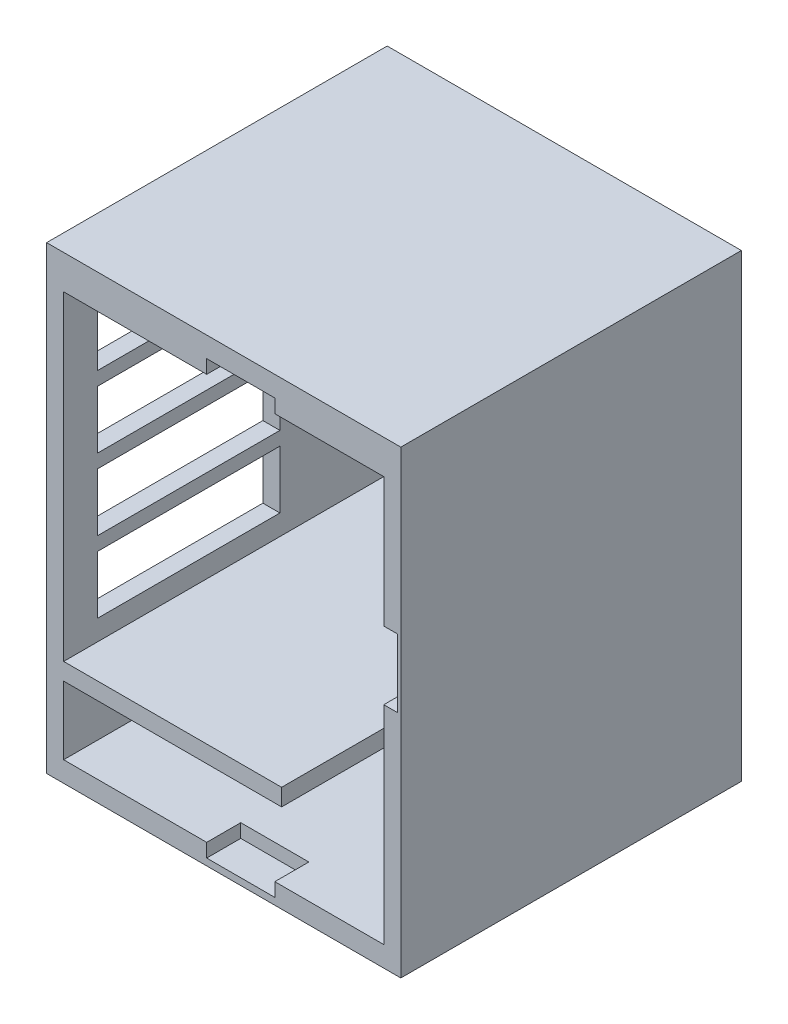
SolidWorks part; units mm, degrees
ref_plane "前基準面" through (0, 0, 0) normal (0, 0, 1) x (1, 0, 0)
ref_plane "上基準面" through (0, 0, 0) normal (0, 1, 0) x (1, 0, 0)
ref_plane "右基準面" through (0, 0, 0) normal (1, 0, 0) x (0, 0, -1)
sketch "草圖1" plane through (0, 0, 0) normal (0, 0, 1) x (1, 0, 0)
  line L5 (-72.8941, 49.2863) -> (31.1059, 49.2863)
  line L6 (-72.8941, 49.2863) -> (-72.8941, -85.7137)
  line L7 (-72.8941, -85.7137) -> (31.1059, -85.7137)
  line L8 (31.1059, 49.2863) -> (31.1059, -85.7137)
  circle A0 centre (-20.8941, -7.7137) radius 47
  dimension "D1" = 94
  dimension "D2" = 52
  dimension "D3" = 104
  dimension "D4" = 135
extrude "填料-伸長2" add sketch "草圖1" along normal blind 100
sketch "草圖2" plane through (0, 0, 100) normal (0, 0, 1) x (1, 0, 0)
  line L0 (31.1059, 49.2863) -> (-72.8941, 49.2863) construction
  line L1 (-67.8941, 39.2863) -> (26.1059, 39.2863)
  line L2 (-67.8941, 39.2863) -> (-67.8941, -54.7137)
  line L3 (-67.8941, -54.7137) -> (26.1059, -54.7137)
  line L4 (26.1059, 39.2863) -> (26.1059, -54.7137)
  line L5 (31.1059, -85.7137) -> (31.1059, 49.2863) construction
  dimension "D1" = 94
  dimension "D2" = 94
  dimension "D3" = 10
  dimension "D4" = 5
extrude "除料-伸長1" cut sketch "草圖2" against normal blind 95
sketch "草圖3" plane through (0, 0, 100) normal (0, 0, 1) x (1, 0, 0)
  line L1 (-67.8941, -59.7137) -> (26.1059, -59.7137)
  line L2 (-67.8941, -59.7137) -> (-67.8941, -79.7137)
  line L3 (-67.8941, -79.7137) -> (26.1059, -79.7137)
  line L4 (26.1059, -59.7137) -> (26.1059, -79.7137)
  line L5 (-72.8941, 49.2863) -> (-72.8941, -85.7137) construction
  line L6 (-67.8941, -54.7137) -> (26.1059, -54.7137) construction
  line L8 (26.1059, -59.7137) -> (-3.8941, -59.7137)
  line L9 (26.1059, -59.7137) -> (26.1059, -54.7137)
  line L10 (26.1059, -54.7137) -> (-3.8941, -54.7137)
  line L11 (-3.8941, -59.7137) -> (-3.8941, -54.7137)
  line M5 (26.1059, -54.7137) -> (-67.8941, -54.7137)
  dimension "D4" = 30
  dimension "D1" = 94
  dimension "D2" = 5
  dimension "D3" = 5
  dimension "D5" = 20
extrude "除料-伸長3" cut sketch "草圖3" against normal blind 70 contours L11 L1 L9 M5 | L4 L1 L2 L3
sketch "草圖4" plane through (0, 0, 100) normal (0, 0, 1) x (1, 0, 0)
  line L0 (31.1059, 49.2863) -> (-72.8941, 49.2863) construction
  line L1 (-67.8941, -79.7137) -> (26.1059, -79.7137) construction
  line L2 (-5.8941, -79.7137) -> (-25.8941, -79.7137)
  line L3 (-5.8941, -79.7137) -> (-5.8941, -83.7137)
  line L4 (-5.8941, -83.7137) -> (-25.8941, -83.7137)
  line L5 (-25.8941, -79.7137) -> (-25.8941, -83.7137)
  line L6 (-72.8941, 49.2863) -> (-72.8941, -85.7137) construction
  line L8 (26.1059, -79.7137) -> (26.1059, 39.2863) construction
  line L9 (26.1059, -18.7137) -> (30.1059, -18.7137)
  line L10 (26.1059, -18.7137) -> (26.1059, 1.2863)
  line L11 (26.1059, 1.2863) -> (30.1059, 1.2863)
  line L12 (30.1059, -18.7137) -> (30.1059, 1.2863)
  line L18 (26.1059, 39.2863) -> (-67.8941, 39.2863) construction
  line L19 (-5.8941, 39.2863) -> (-25.8941, 39.2863)
  line L20 (-5.8941, 39.2863) -> (-5.8941, 43.2863)
  line L21 (-5.8941, 43.2863) -> (-25.8941, 43.2863)
  line L22 (-25.8941, 39.2863) -> (-25.8941, 43.2863)
  line L24 (-72.8941, -85.7137) -> (31.1059, -85.7137) construction
  dimension "D1" = 20
  dimension "D2" = 47
  dimension "D3" = 4
  dimension "D4" = 4
  dimension "D5" = 4
  dimension "D7" = 67
  dimension "D8" = 20
extrude "除料-伸長4" cut sketch "草圖4" against normal blind 10
sketch "草圖6" plane through (-72.8941, 0, 0) normal (-1, 0, 0) x (0, 0, 1)
  line L20 (0, 49.2863) -> (0, -85.7137) construction
  line L21 (90, 31.2863) -> (36.5, 31.2863)
  line L22 (90, 31.2863) -> (90, 14.2863)
  line L23 (90, 14.2863) -> (36.5, 14.2863)
  line L24 (36.5, 31.2863) -> (36.5, 14.2863)
  line L25 (100, 49.2863) -> (0, 49.2863) construction
  line L27 (90, 10.2863) -> (36.5, 10.2863)
  line L28 (90, 10.2863) -> (90, -6.7137)
  line L29 (90, -6.7137) -> (36.5, -6.7137)
  line L30 (36.5, 10.2863) -> (36.5, -6.7137)
  line L31 (90, -10.7137) -> (36.5, -10.7137)
  line L32 (90, -10.7137) -> (90, -27.7137)
  line L33 (90, -27.7137) -> (36.5, -27.7137)
  line L34 (36.5, -10.7137) -> (36.5, -27.7137)
  line L35 (90, -31.7137) -> (36.5, -31.7137)
  line L36 (90, -31.7137) -> (90, -48.7137)
  line L37 (90, -48.7137) -> (36.5, -48.7137)
  line L38 (36.5, -31.7137) -> (36.5, -48.7137)
  dimension "D1" = 17
  dimension "D2" = 53.5
  dimension "D3" = 36.5
  dimension "D4" = 18
  dimension "D5" = 17
  dimension "D6" = 17
  dimension "D7" = 17
  dimension "D8" = 4
  dimension "D9" = 4
  dimension "D10" = 4
  dimension "D11" = 53.5
  dimension "D12" = 53.5
  dimension "D13" = 53.5
  dimension "D14" = 36.5
extrude "除料-伸長6" cut sketch "草圖6" against normal up to next
sketch "草圖7" plane through (0, -85.7137, 0) normal (0, -1, 0) x (1, 0, 0)
  line L0 (31.1059, 100) -> (31.1059, 0) construction
  line L1 (11.1059, 43) -> (-0.8941, 43)
  line L2 (11.1059, 43) -> (11.1059, 55)
  line L3 (11.1059, 55) -> (-0.8941, 55)
  line L4 (-0.8941, 43) -> (-0.8941, 55)
  line L5 (-72.8941, 100) -> (31.1059, 100) construction
  line L6 (-72.8941, 100) -> (-72.8941, 0) construction
  line L7 (-52.8941, 43) -> (-40.8941, 43)
  line L8 (-52.8941, 43) -> (-52.8941, 55)
  line L9 (-52.8941, 55) -> (-40.8941, 55)
  line L10 (-40.8941, 43) -> (-40.8941, 55)
  dimension "D1" = 12
  dimension "D2" = 12
  dimension "D3" = 20
  dimension "D4" = 45
  dimension "D5" = 20
  dimension "12" = 12
  dimension "D7" = 12
  dimension "D8" = 45
extrude "除料-伸長7" cut sketch "草圖7" against normal up to next
